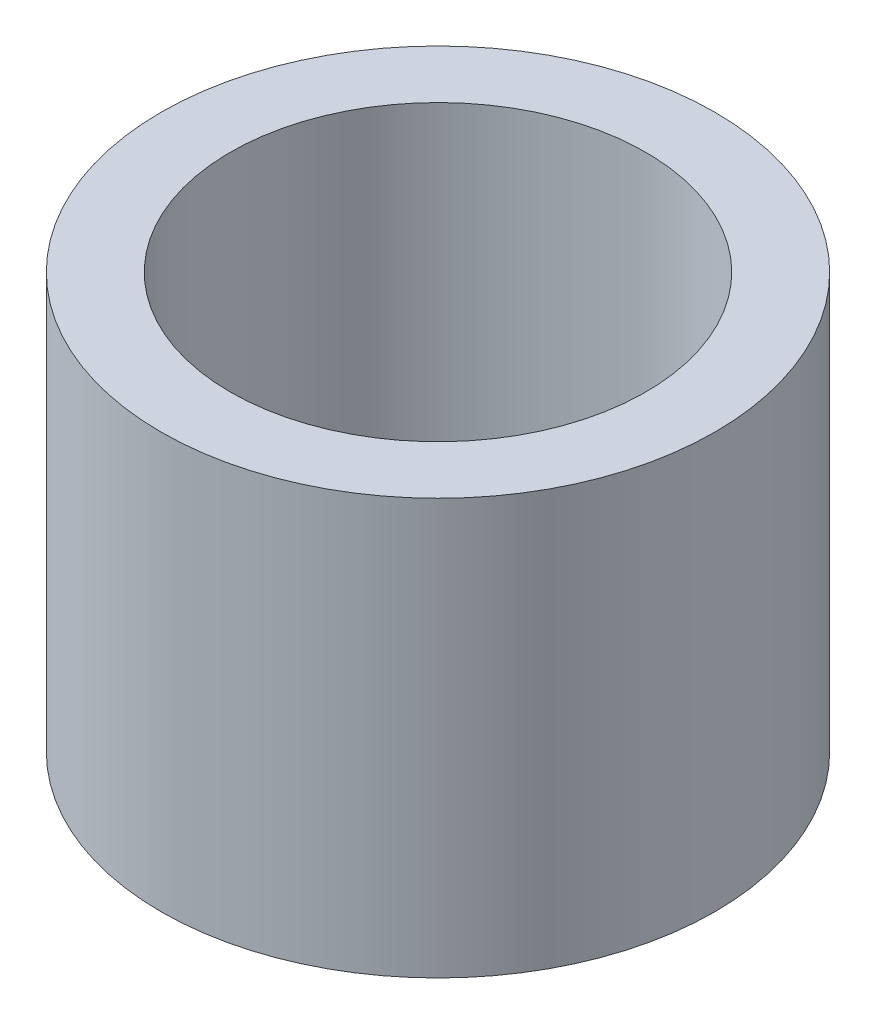
SolidWorks part; units mm, degrees
ref_plane "Front Plane" through (0, 0, 0) normal (0, 0, 1) x (1, 0, 0)
ref_plane "Top Plane" through (0, 0, 0) normal (0, 1, 0) x (1, 0, 0)
ref_plane "Right Plane" through (0, 0, 0) normal (1, 0, 0) x (0, 0, -1)
sketch "Sketch1" plane through (0, 0, 0) normal (0, 1, 0) x (1, 0, 0)
  circle A0 centre (-5.4251, 4.3107) radius 10
  dimension "D1" = 20
extrude "Boss-Extrude1" add sketch "Sketch1" along normal blind 15
sketch "Sketch2" plane through (0, 15, 0) normal (0, 1, 0) x (1, 0, 0)
  circle A0 centre (-5.4251, 4.3107) radius 7.5
  circle A1 centre (-5.4251, 4.3107) radius 10 construction
  dimension "D1" = 15
extrude "Cut-Extrude1" cut sketch "Sketch2" against normal blind 12.5
